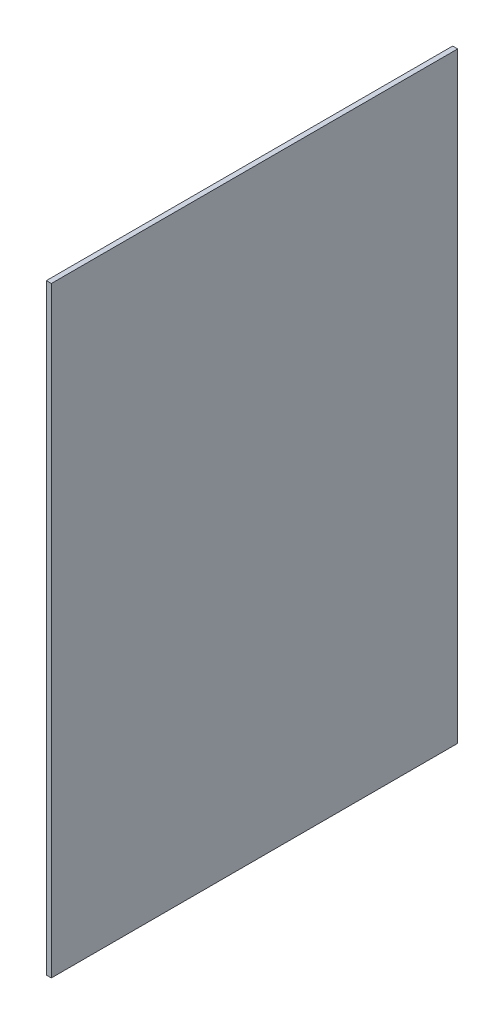
SolidWorks part; units mm, degrees
ref_plane "Front Plane" through (0, 0, 0) normal (0, 0, 1) x (1, 0, 0)
ref_plane "Top Plane" through (0, 0, 0) normal (0, 1, 0) x (1, 0, 0)
ref_plane "Right Plane" through (0, 0, 0) normal (1, 0, 0) x (0, 0, -1)
sketch "Sketch2" plane through (0, 0, 0) normal (1, 0, 0) x (0, 0, -1)
  line L1 (-42.9302, 447.7312) -> (274.5698, 447.7312)
  line L2 (-42.9302, 447.7312) -> (-42.9302, -22.1688)
  line L3 (-42.9302, -22.1688) -> (274.5698, -22.1688)
  line L4 (274.5698, 447.7312) -> (274.5698, -22.1688)
extrude "Boss-Extrude1" add sketch "Sketch2" along normal blind 3.9 contours L2 L1 L4 L3
